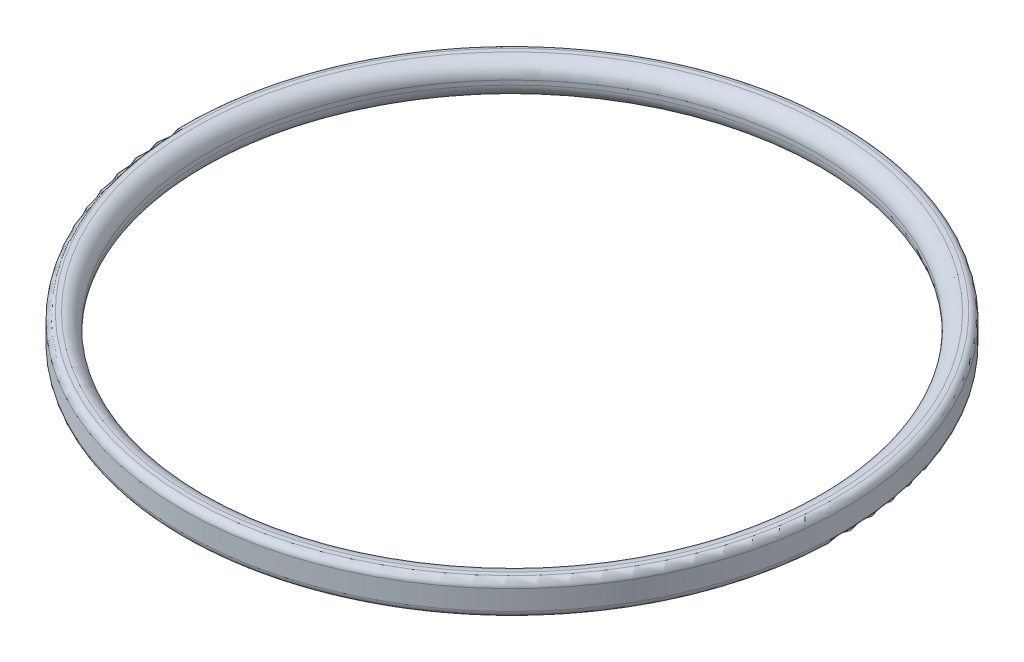
SolidWorks part; units mm, degrees
ref_plane "Front Plane" through (0, 0, 0) normal (0, 0, 1) x (1, 0, 0)
ref_plane "Top Plane" through (0, 0, 0) normal (0, 1, 0) x (1, 0, 0)
ref_plane "Right Plane" through (0, 0, 0) normal (1, 0, 0) x (0, 0, -1)
ref_axis "Axis1" through (0, -55, 0) along (0, 1, 0)
sketch "Sketch2" plane through (0, 0, 0) normal (0, 0, 1) x (1, 0, 0)
  line L1 (38.1, 0) -> (35.179, 0)
  line L2 (35.179, 0) -> (35.179, 3.81)
  line L3 (35.179, 3.81) -> (38.1, 3.81)
  line L4 (38.1, 3.81) -> (38.1, 0)
  dimension "D1" = 3.81
  dimension "D2" = 2.921
revolve "Revolve1" add sketch "Sketch2" angle 360 about axis through (0, -55, 0) along (0, 1, 0)
fillet "Fillet1" radius 1.651 2 edges at (0, 0, -35.179) (0, 3.81, -35.179)
fillet "Fillet3" radius 0.762 2 edges at (0, 0, -38.1) (0, 3.81, -38.1)
